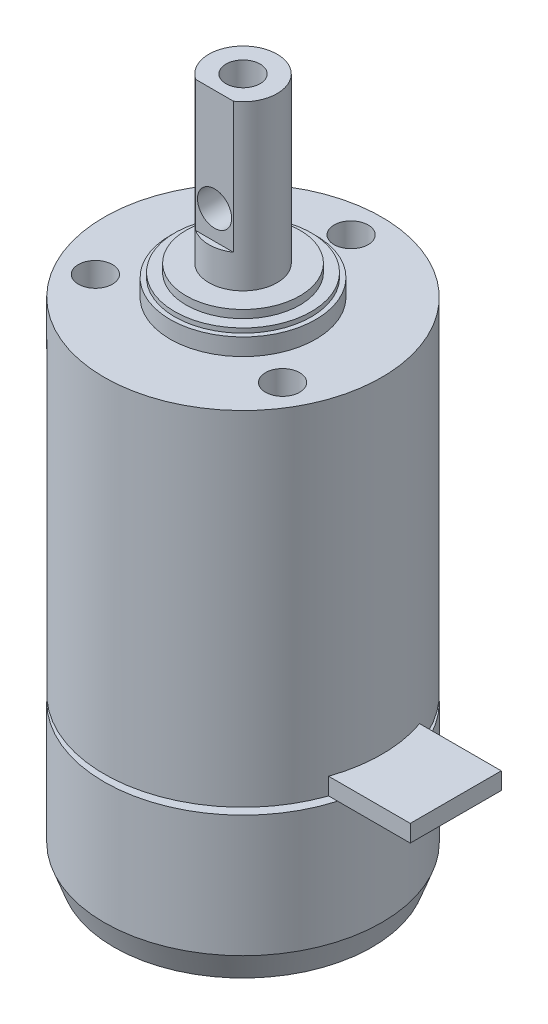
SolidWorks part; units mm, degrees
ref_plane "前视基准面" through (0, 0, 0) normal (0, 0, 1) x (1, 0, 0)
ref_plane "上视基准面" through (0, 0, 0) normal (0, 1, 0) x (1, 0, 0)
ref_plane "右视基准面" through (0, 0, 0) normal (1, 0, 0) x (0, 0, -1)
sketch "草图1" plane through (0, 0, 0) normal (0, 1, 0) x (1, 0, 0)
  circle A0 centre (0, 0) radius 12.2
  dimension "D1" = 24.4
extrude "凸台-拉伸1" add sketch "草图1" along normal blind 43.8
sketch "草图2" plane through (0, 43.8, 0) normal (0, 1, 0) x (1, 0, 0)
  circle A0 centre (0, 0) radius 9.5
  dimension "D1" = 19
sketch "草图3" plane through (0, 43.8, 0) normal (0, 1, 0) x (1, 0, 0)
  line L0 (0, 9.5) -> (0, 0) construction
  line L1 (0, 0) -> (-8.2272, -4.75) construction
  line L2 (-8.2272, -4.75) -> (-6.7272, -4.75) construction
  line L3 (8.2272, -4.75) -> (0, 0) construction
  line L4 (6.7272, -4.75) -> (8.2272, -4.75) construction
  circle A0 centre (0, 9.5) radius 1.5
  circle A1 centre (0, 0) radius 9.5 construction
  circle A2 centre (-8.2272, -4.75) radius 1.5
  circle A3 centre (8.2272, -4.75) radius 1.5
  dimension "D2" = 3
  dimension "D3" = 3
  dimension "D4" = 3
  dimension "D1" = 120
extrude "切除-拉伸1" cut sketch "草图3" against normal blind 4
chamfer "倒角1" distance 0.85 distance2 2.3 1 edges at (0, 0, 12.2)
sketch "草图4" plane through (0, 43.8, 0) normal (0, 1, 0) x (1, 0, 0)
  circle A0 centre (0, 0) radius 6.4
  dimension "D1" = 12.8
extrude "凸台-拉伸2" add sketch "草图4" along normal blind 1.5
sketch "草图5" plane through (0, 45.3, 0) normal (0, 1, 0) x (1, 0, 0)
  circle A0 centre (0, 0) radius 6
  dimension "D1" = 12
extrude "凸台-拉伸3" add sketch "草图5" along normal blind 0.4
sketch "草图6" plane through (0, 45.7, 0) normal (0, 1, 0) x (1, 0, 0)
  circle A0 centre (0, 0) radius 5
  dimension "D1" = 10
extrude "凸台-拉伸4" add sketch "草图6" along normal blind 0.7
sketch "草图7" plane through (0, 46.4, 0) normal (0, 1, 0) x (1, 0, 0)
  circle A0 centre (0, 0) radius 3
  dimension "D1" = 6
extrude "凸台-拉伸5" add sketch "草图7" along normal blind 14.4
sketch "草图8" plane through (0, 60.8, 0) normal (0, 1, 0) x (1, 0, 0)
  circle A0 centre (0, 0) radius 1.5
  dimension "D1" = 3
extrude "切除-拉伸2" cut sketch "草图8" against normal blind 5.5
sketch "草图9" plane through (0, 60.8, 0) normal (0, 1, 0) x (1, 0, 0)
  line L0 (-1.6583, -2.5) -> (1.6583, -2.5)
  arc A0 (-1.6583, -2.5) -> (1.6583, -2.5) centre (0, 0) ccw
  dimension "D2" = 6
  dimension "D1" = 2.5
extrude "切除-拉伸3" cut sketch "草图9" against normal blind 11.5
sketch "草图10" plane through (0, 0, 2.5) normal (0, 0, 1) x (1, 0, 0)
  line L0 (1.6583, 60.8) -> (-1.6583, 60.8) construction
  line L1 (-1.6583, 49.3) -> (-1.6583, 60.8) construction
  circle A0 centre (0, 51.8) radius 1.5
  dimension "D2" = 3
  dimension "D1" = 9
  dimension "D3" = 1.6583
extrude "切除-拉伸4" cut sketch "草图10" against normal through all
sketch "草图11" plane through (0, 0, 0) normal (0, -1, 0) x (1, 0, 0)
  circle A0 centre (0, 0) radius 12.2
  circle A1 centre (0, 0) radius 7
  dimension "D1" = 14
  dimension "D2" = 24.4
extrude "切除-拉伸5" cut sketch "草图11" against normal blind 0.6 from offset 13 offset against normal yes
ref_plane "基准面1" through (18.7, 0, 0) normal (1, 0, 0) x (0, 0, -1)
sketch "草图12" plane through (18.7, 0, 0) normal (1, 0, 0) x (0, 0, -1)
  line L0 (-12.2, 13.6) -> (12.2, 13.6) construction
  line L1 (-4, 13.6) -> (4, 13.6)
  line L2 (-4, 13.6) -> (-4, 15.1)
  line L3 (-4, 15.1) -> (4, 15.1)
  line L4 (4, 13.6) -> (4, 15.1)
  dimension "D1" = 8
  dimension "D2" = 1.5
  dimension "D3" = 4
extrude "凸台-拉伸6" add sketch "草图12" against normal up to next
sketch "草图13" plane through (0, 0, 0) normal (0, -1, 0) x (1, 0, 0)
  line L0 (0, 5.5) -> (0, 0) construction
  line L1 (0, 0) -> (-4.7631, -2.75) construction
  line L3 (4.7631, -2.75) -> (0, 0) construction
  circle A0 centre (0, 0) radius 5.5
  circle A1 centre (0, 5.5) radius 1
  circle A2 centre (-4.7631, -2.75) radius 1
  circle A3 centre (4.7631, -2.75) radius 1
  dimension "D1" = 11
  dimension "D2" = 2
  dimension "D3" = 2
  dimension "D4" = 2
  dimension "D5" = 120
  dimension "D6" = 120
extrude "切除-拉伸6" cut sketch "草图13" against normal blind 3 contours A0 A1 | A0 A1 | A0 A2 | A0 A2 | A0 A3 | A0 A3
sketch "草图14" plane through (0, 0, 0) normal (0, -1, 0) x (1, 0, 0)
  circle A0 centre (0, 0) radius 3
  dimension "D1" = 6
extrude "凸台-拉伸7" add sketch "草图14" along normal blind 4
chamfer "倒角2" distance 0.2 distance2 0.1 1 edges at (0, -4, -3)
